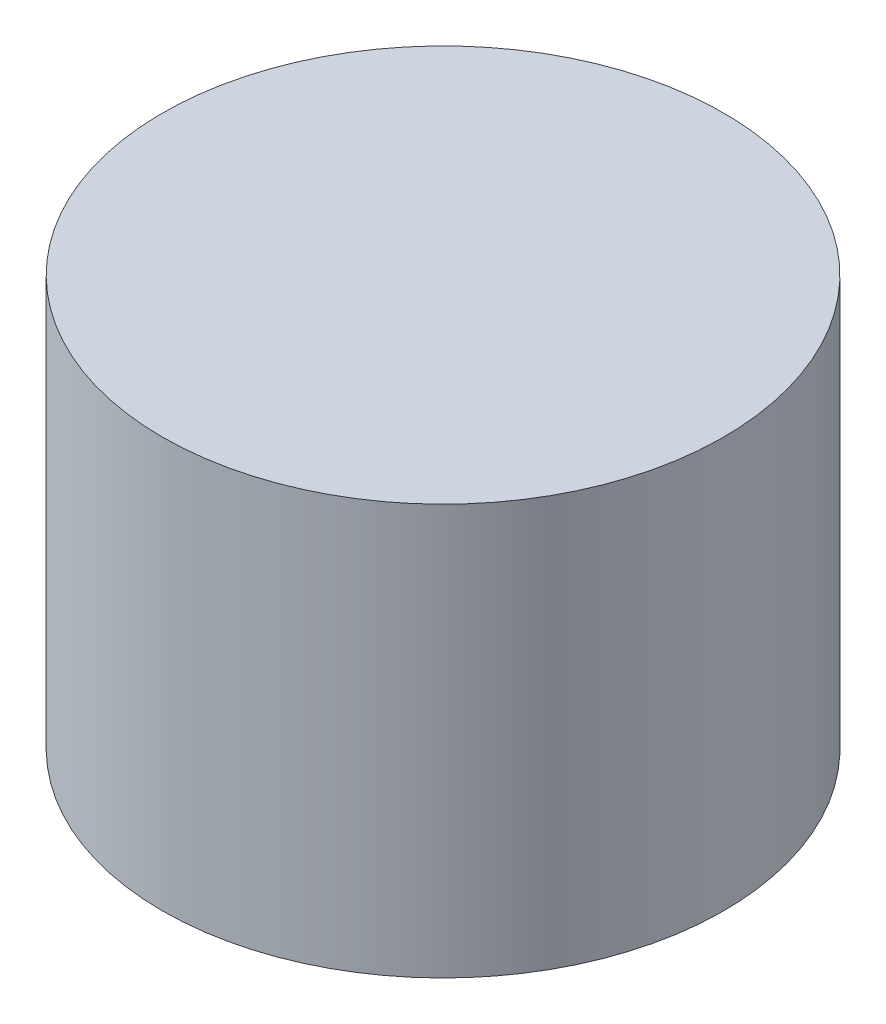
SolidWorks part; units mm, degrees
ref_plane "Front Plane" through (0, 0, 0) normal (0, 0, 1) x (1, 0, 0)
ref_plane "Top Plane" through (0, 0, 0) normal (0, 1, 0) x (1, 0, 0)
ref_plane "Right Plane" through (0, 0, 0) normal (1, 0, 0) x (0, 0, -1)
sketch "Sketch1" plane through (0, 0, 0) normal (0, 1, 0) x (1, 0, 0)
  circle A0 centre (0, 0) radius 20.6375
  dimension "D1" = 41.275
extrude "Boss-Extrude1" add sketch "Sketch1" along normal blind 30.1752
